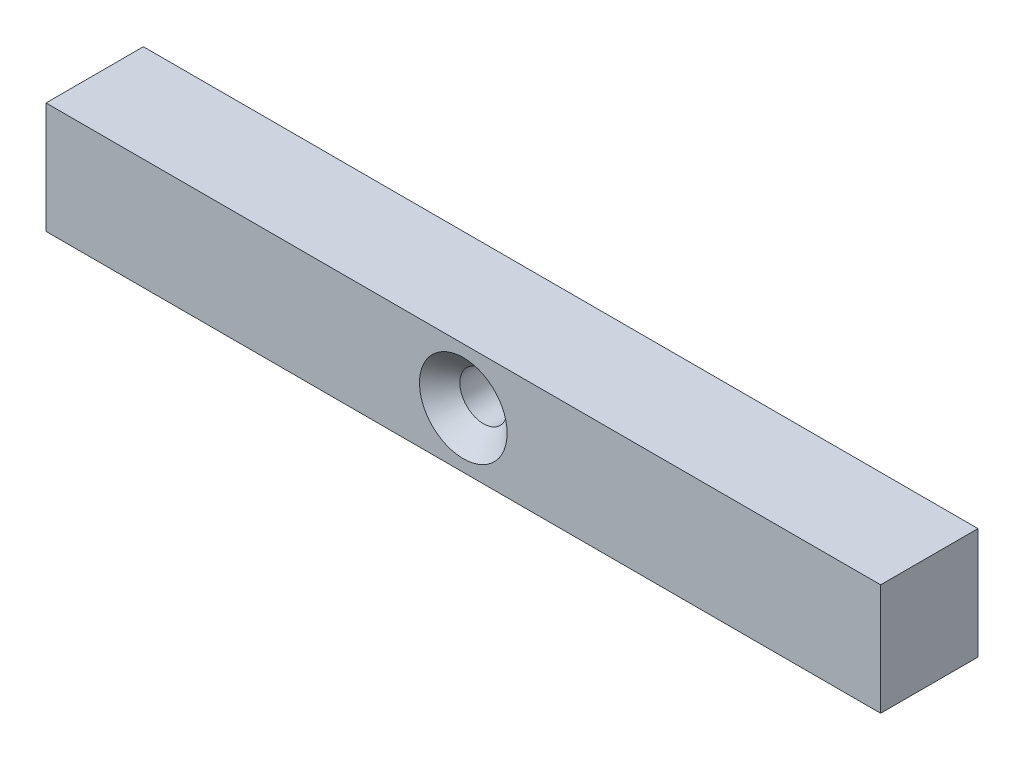
SolidWorks part; units mm, degrees
material "Plain Carbon Steel"
ref_plane "Front Plane" through (0, 0, 0) normal (0, 0, 1) x (1, 0, 0)
ref_plane "Top Plane" through (0, 0, 0) normal (0, 1, 0) x (1, 0, 0)
ref_plane "Right Plane" through (0, 0, 0) normal (1, 0, 0) x (0, 0, -1)
sketch "Sketch1" plane through (0, 0, 0) normal (0, 0, 1) x (1, 0, 0)
  line L1 (-30, -4) -> (30, -4)
  line L2 (-30, -4) -> (-30, 4)
  line L3 (-30, 4) -> (30, 4)
  line L4 (30, -4) -> (30, 4)
  line L5 (-30, -4) -> (30, 4) construction
  line L6 (-30, 4) -> (30, -4) construction
  point P0 (0, 0)
  dimension "D1" = 8
  dimension "D2" = 60
extrude "Boss-Extrude1" add sketch "Sketch1" along normal blind 7
sketch "Sketch2" plane through (0, 0, 7) normal (0, 0, 1) x (1, 0, 0)
  point P0 (0, 0)
hole_wizard "CSK for M3 Countersunk Flat Head Screw1" positions "Sketch3" profile "Sketch4" countersink size "M3" standard "ISO" end condition through all
sketch "Sketch3" plane through (0, 0, 7) normal (0, 0, 1) x (1, 0, 0)
  point P0 (0, 0)
sketch "Sketch4" plane through (0, 0, 7) normal (1, 0, 0) x (0, -1, 0)
  line L0 (0, 0) -> (0, 7)
  line L1 (0, 7) -> (1.7, 7)
  line L2 (1.7, 7) -> (1.7, 1.45)
  line L3 (1.7, 1.45) -> (3.15, 0)
  line L5 (3.15, 0) -> (0, 0)
  line L6 (-1.7, 1.45) -> (-3.15, 0) construction
  line L11 (0, -6.35) -> (0, 107.95) construction
  dimension "Thru Hole Dia." = 3.4
  dimension "Thru Hole Depth" = 7
  dimension "Near C'Sink Dia." = 6.3
  dimension "Near C'Sink Angle" = 90
